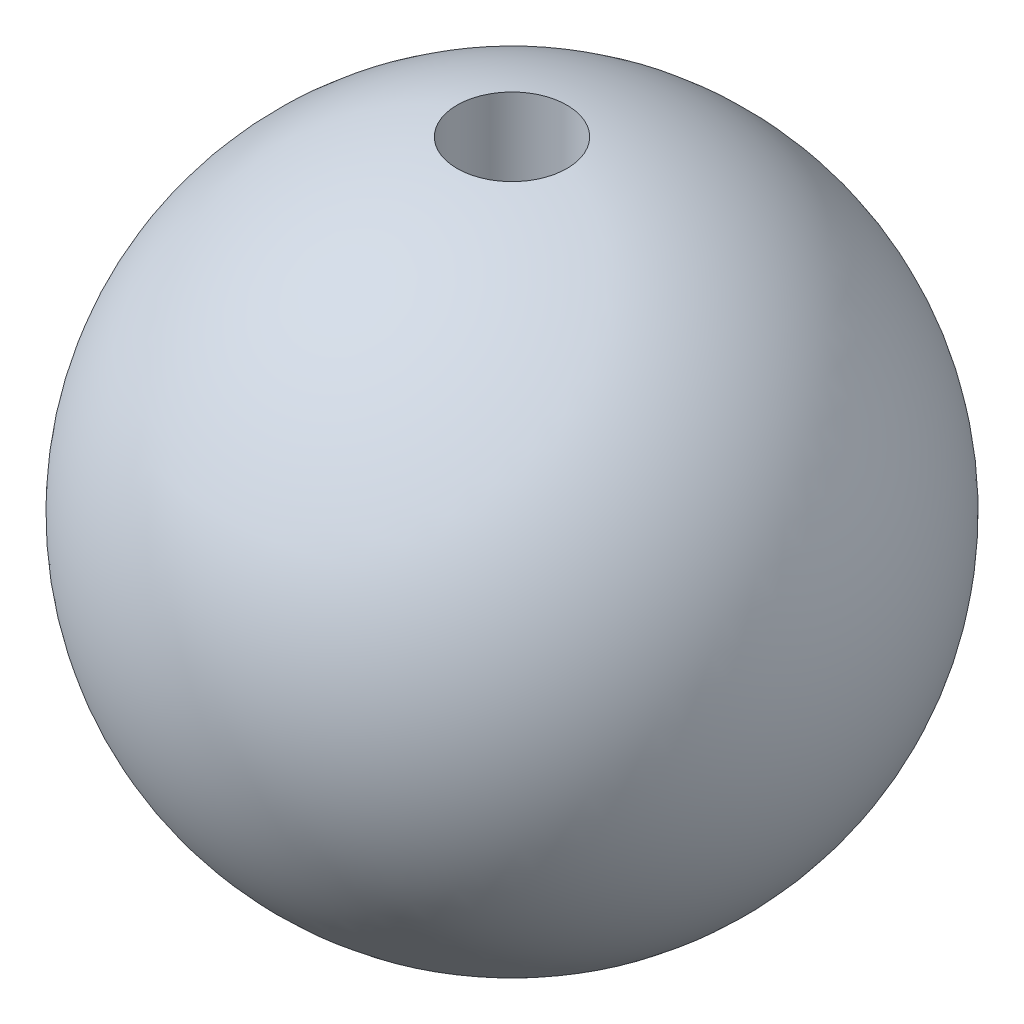
SolidWorks part; units mm, degrees
ref_plane "前视基准面" through (0, 0, 0) normal (0, 0, 1) x (1, 0, 0)
ref_plane "上视基准面" through (0, 0, 0) normal (0, 1, 0) x (1, 0, 0)
ref_plane "右视基准面" through (0, 0, 0) normal (1, 0, 0) x (0, 0, -1)
other "Configuration Table"
sketch "草图1" plane through (0, 0, 0) normal (0, 0, 1) x (1, 0, 0)
  line L0 (0, 30) -> (0, -30) construction
  line L1 (-5, 29.5804) -> (-5, -29.5804) construction
  line L2 (5, 29.5804) -> (5, -29.5804) construction
  line L3 (-5, 29.5804) -> (-5, 0)
  line L4 (-5, 0) -> (0, 0)
  line L5 (0, 0) -> (0, -30)
  circle A0 centre (0, 0) radius 30 construction
  arc A1 (-5, 29.5804) -> (0, -30) centre (0, 0) ccw
  dimension "D1" = 60
  dimension "D2" = 10
revolve "旋转4" add sketch "草图1" angle 360 about L0
